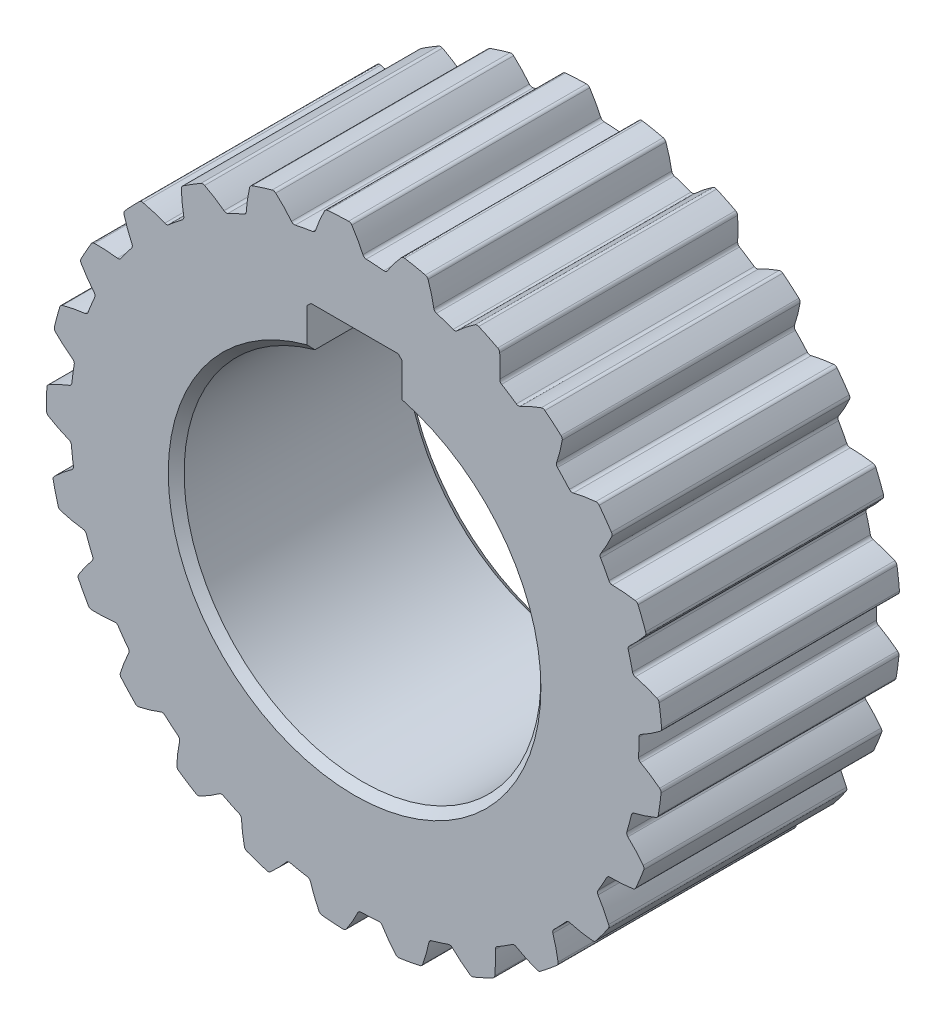
SolidWorks part; units mm, degrees
material "1.6587 (18CrNiMo7-6)"
ref_plane "Front Plane" through (0, 0, 0) normal (0, 0, 1) x (1, 0, 0)
ref_plane "Top Plane" through (0, 0, 0) normal (0, 1, 0) x (1, 0, 0)
ref_plane "Right Plane" through (0, 0, 0) normal (1, 0, 0) x (0, 0, -1)
sketch "Sketch1" plane through (0, 0, 0) normal (0, 0, 1) x (1, 0, 0)
  line L0 (0, 0) -> (0, 27.5) construction
  line L1 (6, 21.6852) -> (6, 27.5)
  line L2 (-6, 21.6852) -> (-6, 27.5)
  line L4 (6, 27.5) -> (-6, 27.5)
  line L5 (6, 0) -> (6, 27.5) construction
  line L6 (-6, 0) -> (-6, 27.5) construction
  arc A0 (-6, 21.6852) -> (6, 21.6852) centre (0, 0) ccw
  circle A1 centre (0, 0) radius 35.85
  dimension "D1" = 45
  dimension "D2" = 27.5
  dimension "D5" = 71.7
  dimension "D3" = 6
  dimension "D4" = 6
extrude "Boss-Extrude1" add sketch "Sketch1" along normal blind 30
sketch "Sketch2" plane through (0, 0, 0) normal (0, 0, 1) x (1, 0, 0)
  line L0 (0, 0) -> (37.4458, 2.0146) construction
  line L1 (0, 0) -> (43.1943, 5.0586) construction
  circle A0 centre (0, 0) radius 37.5 construction
  arc A1 (35.8337, 1.0823) -> (35.1141, 7.2266) centre (0, 0) ccw
  arc A2 (38.7391, 2.9334) -> (38.3686, 6.0969) centre (0, 0) ccw
  spline S0 degree 4 poles (32.476, 0) (32.4878, 0.0002) (32.5208, 0.0012) (32.5831, 0.0053) (32.6846, 0.0149) (32.8137, 0.0317) (32.9801, 0.0585) (33.1755, 0.0965) (33.3894, 0.1451) (33.621, 0.2054) (33.8511, 0.2719) (34.0795, 0.3443) (34.306, 0.4218) (34.5791, 0.522) (34.9046, 0.651) (35.282, 0.8145) (35.7061, 1.0148) (36.1339, 1.2349) (36.551, 1.4643) (36.9676, 1.7109) (37.3672, 1.9599) (37.7769, 2.2334) (38.1524, 2.4934) (38.5668, 2.801) (38.8993, 3.0539) (39.3308, 3.4046) (39.5835, 3.6168) (39.8766, 3.8709) (40.0054, 3.9868) (40.0847, 4.0581) knots 0 0 0 0 0 0.005377 0.015084 0.028532 0.04661 0.064855 0.092111 0.119476 0.146842 0.174209 0.201575 0.228941 0.256307 0.307035 0.361767 0.4165 0.471232 0.525964 0.580697 0.635429 0.690161 0.744894 0.799626 0.854358 0.909091 0.954545 1 1 1 1 1 construction
  spline S1 degree 4 poles (35.8337, 1.0823) (35.8551, 1.0931) (35.9835, 1.1583) (36.2172, 1.2807) (36.551, 1.4643) (36.9676, 1.7109) (37.3672, 1.9599) (37.7769, 2.2334) (38.1524, 2.4934) (38.4645, 2.725) (38.6453, 2.8613) (38.738, 2.9325) (38.7391, 2.9334) knots 0.405523 0.405523 0.405523 0.405523 0.405523 0.4165 0.471232 0.525964 0.580697 0.635429 0.690161 0.744894 0.799626 0.800307 0.800307 0.800307 0.800307 0.800307
  spline S2 degree 4 poles (35.1141, 7.2266) (35.1375, 7.221) (35.2774, 7.1873) (35.5331, 7.1222) (35.9002, 7.0206) (36.3625, 6.877) (36.8089, 6.7271) (37.2707, 6.5556) (37.6962, 6.3894) (38.0533, 6.2362) (38.2607, 6.1453) (38.3673, 6.0975) (38.3686, 6.0969) knots 0.405523 0.405523 0.405523 0.405523 0.405523 0.4165 0.471232 0.525964 0.580697 0.635429 0.690161 0.744894 0.799626 0.800307 0.800307 0.800307 0.800307 0.800307
  dimension "D1" = 75
  dimension "D2" = 71.7
  dimension "D3" = 77.7
  dimension "D4" = 3.6
extrude "Boss-Extrude2" add sketch "Sketch2" along normal blind 30
fillet "Fillet1" radius 0.48 4 edges at (35.8337, 1.0823, 15) (38.7391, 2.9334, 15) (38.3686, 6.0969, 15) (35.1141, 7.2266, 15)
pattern_circular "CirPattern1" count 25 over 360 about axis through (0, 0, 30) along (0, 0, -1) of "Boss-Extrude2", "Fillet1"
chamfer "Chamfer1" distance 0.5 2 edges at (6, 27.5, 15) (-6, 27.5, 15)
chamfer "Chamfer2" distance 1 2 edges at (0, -22.5, 0) (0, -22.5, 30)
